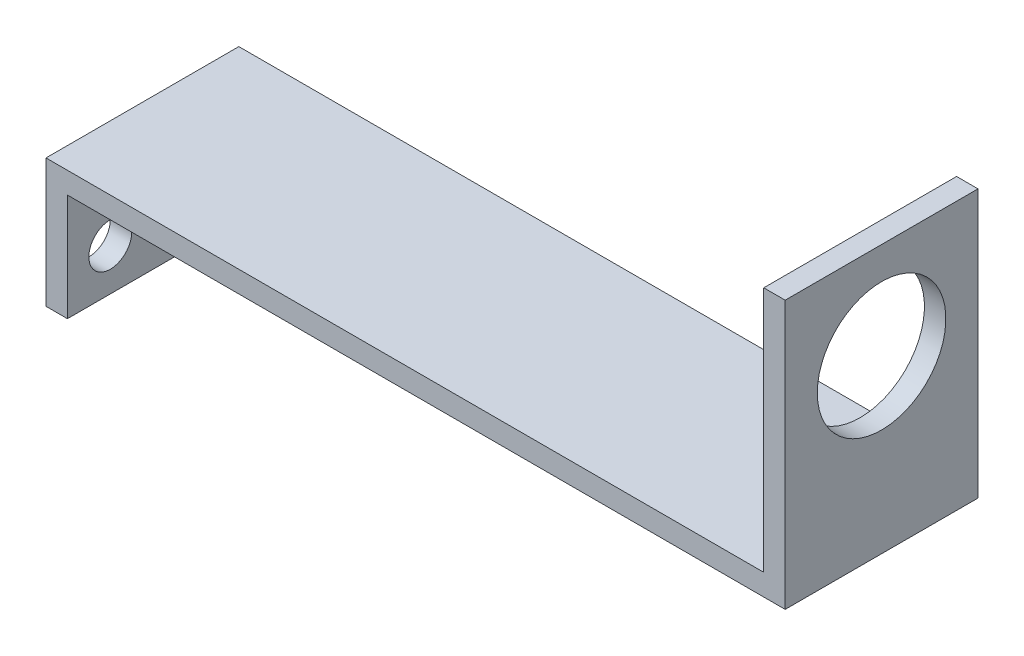
SolidWorks part; units mm, degrees
ref_plane "Front Plane" through (0, 0, 0) normal (0, 0, 1) x (1, 0, 0)
ref_plane "Top Plane" through (0, 0, 0) normal (0, 1, 0) x (1, 0, 0)
ref_plane "Right Plane" through (0, 0, 0) normal (1, 0, 0) x (0, 0, -1)
sketch "Sketch1" plane through (0, 0, 0) normal (0, 0, 1) x (1, 0, 0)
  line L0 (0, 0) -> (0, 12)
  line L1 (0, 12) -> (67, 12)
  line L2 (67, 12) -> (67, 35)
  line L3 (67, 35) -> (69, 35)
  line L4 (69, 35) -> (69, 10)
  line L5 (69, 10) -> (2, 10)
  line L6 (2, 10) -> (2, 0)
  line L7 (2, 0) -> (0, 0)
  dimension "D1" = 12
  dimension "D2" = 67
  dimension "D3" = 23
  dimension "D4" = 2
  dimension "D5" = 2
  dimension "D6" = 2
extrude "Boss-Extrude1" add sketch "Sketch1" along normal blind 18
sketch "Sketch2" plane through (0, 0, 0) normal (-1, 0, 0) x (0, 0, 1)
  line L0 (-5.9487, 4) -> (24.1871, 4) construction
  line L1 (4, -3.3538) -> (4, 10.3991) construction
  line L2 (14, -3.3538) -> (14, 10.3991) construction
  line L3 (18, 0) -> (0, 0) construction
  line L4 (18, 12) -> (18, 0) construction
  line L5 (0, 12) -> (0, 0) construction
  circle A0 centre (4, 4) radius 2
  circle A1 centre (14, 4) radius 2
  dimension "D4" = 4
  dimension "D5" = 4
  dimension "D1" = 4
  dimension "D2" = 4
  dimension "D3" = 4
extrude "Cut-Extrude1" cut sketch "Sketch2" against normal up to next
sketch "Sketch3" plane through (67, 0, 0) normal (-1, 0, 0) x (0, 0, 1)
  line L0 (9, 35.7048) -> (9, 16.4715) construction
  line L1 (18, 35) -> (0, 35) construction
  circle A0 centre (9, 26) radius 6
  point P6 (9, 35)
  dimension "D1" = 12
  dimension "D2" = 9
extrude "Cut-Extrude2" cut sketch "Sketch3" against normal up to next contours A0
